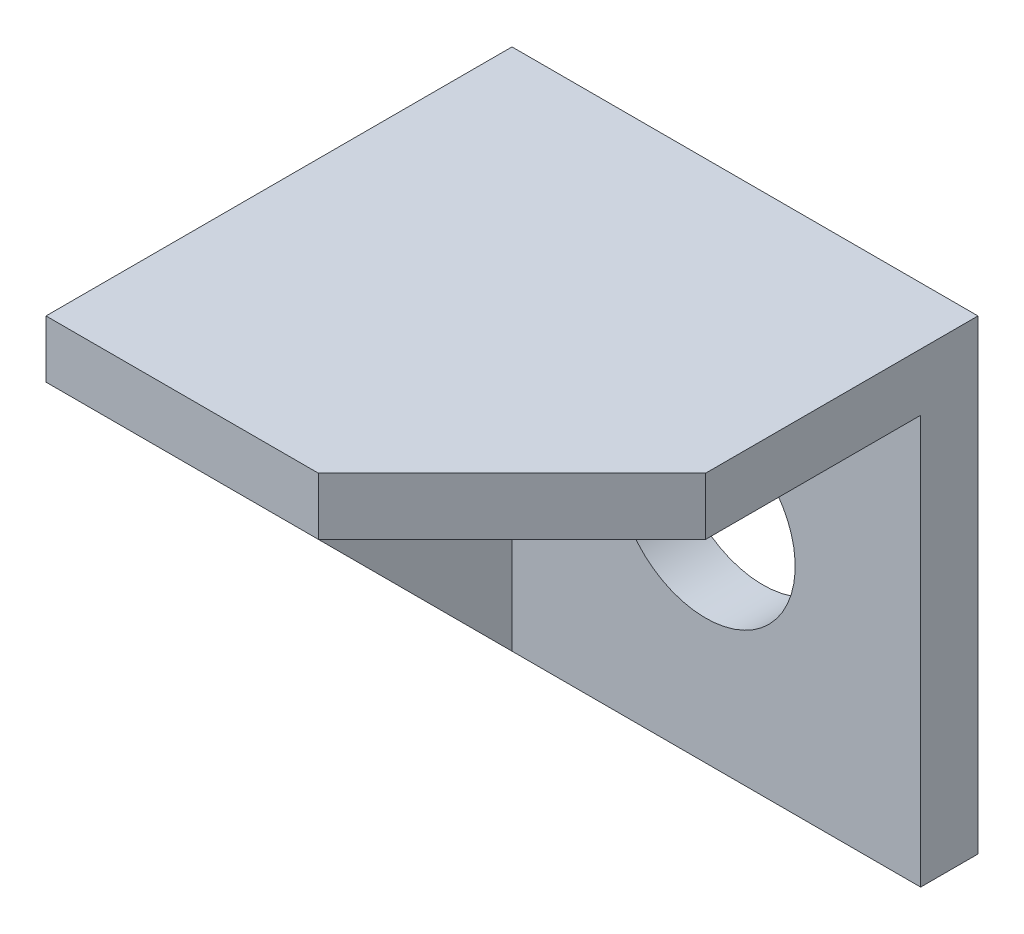
SolidWorks part; units mm, degrees
ref_plane "Front Plane" through (0, 0, 0) normal (0, 0, 1) x (1, 0, 0)
ref_plane "Top Plane" through (0, 0, 0) normal (0, 1, 0) x (1, 0, 0)
ref_plane "Right Plane" through (0, 0, 0) normal (1, 0, 0) x (0, 0, -1)
sketch "Sketch2" plane through (0, 0, 0) normal (0, 0, 1) x (1, 0, 0)
  line L1 (-32.5, -32.5) -> (32.5, -32.5)
  line L2 (-32.5, -32.5) -> (-32.5, 32.5)
  line L3 (-32.5, 32.5) -> (32.5, 32.5)
  line L4 (32.5, -32.5) -> (32.5, 32.5)
  line L5 (-32.5, -32.5) -> (32.5, 32.5) construction
  line L6 (-32.5, 32.5) -> (32.5, -32.5) construction
  point P0 (0, 0)
  dimension "D1" = 65
  dimension "D2" = 65
extrude "Boss-Extrude1" add sketch "Sketch2" along normal blind 65
sketch "Sketch3" plane through (0, 0, 65) normal (0, 0, 1) x (1, 0, 0)
  line L0 (32.5, -32.5) -> (-24.5, -32.5)
  line L1 (-32.5, -32.5) -> (32.5, -32.5) construction
  line L2 (-24.5, -32.5) -> (-24.5, 24.5)
  line L3 (-24.5, 24.5) -> (32.5, 24.5)
  line L4 (32.5, -32.5) -> (32.5, 32.5) construction
  line L5 (32.5, 24.5) -> (32.5, -32.5)
  dimension "D1" = 57
  dimension "D2" = 57
extrude "Cut-Extrude1" cut sketch "Sketch3" against normal blind 57
ref_plane "Plane5" through (-24.5, -32.5, 8) normal (0, 0, 1) x (1, 0, 0)
sketch "Sketch5" plane through (-24.5, 0, 0) normal (1, 0, 0) x (0, 0, -1)
  line L0 (-65, -32.5) -> (-65, 24.5)
  line L1 (-65, 24.5) -> (-8, -32.5)
  line L2 (-8, -16.825) -> (-8, -48.175) construction
  line L3 (-8, -32.5) -> (0, -32.5) construction
  line L4 (-8, -32.5) -> (-65, -32.5)
extrude "Cut-Extrude2" cut sketch "Sketch5" against normal through all
sketch "Sketch7" plane through (0, 24.5, 0) normal (0, -1, 0) x (-1, 0, 0)
  line L0 (-32.5, -65) -> (-5.5, -65)
  line L1 (-32.5, -65) -> (24.5, -65) construction
  line L2 (-5.5, -65) -> (-32.5, -38)
  line L3 (-32.5, -8) -> (-32.5, -65) construction
  line L4 (-32.5, -38) -> (-32.5, -65)
  dimension "D1" = 27
  dimension "D2" = 45
extrude "Cut-Extrude3" cut sketch "Sketch7" against normal through all
sketch "Sketch8" plane through (0, 0, 0) normal (0, 0, -1) x (-1, 0, 0)
  line L2 (-32.5, -32.5) -> (-32.5, 32.5) construction
  circle A0 centre (-2.5, -2.5) radius 12.5
  dimension "D1" = 25
  dimension "D2" = 30
  dimension "D3" = 30
extrude "Cut-Extrude4" cut sketch "Sketch8" against normal through all
